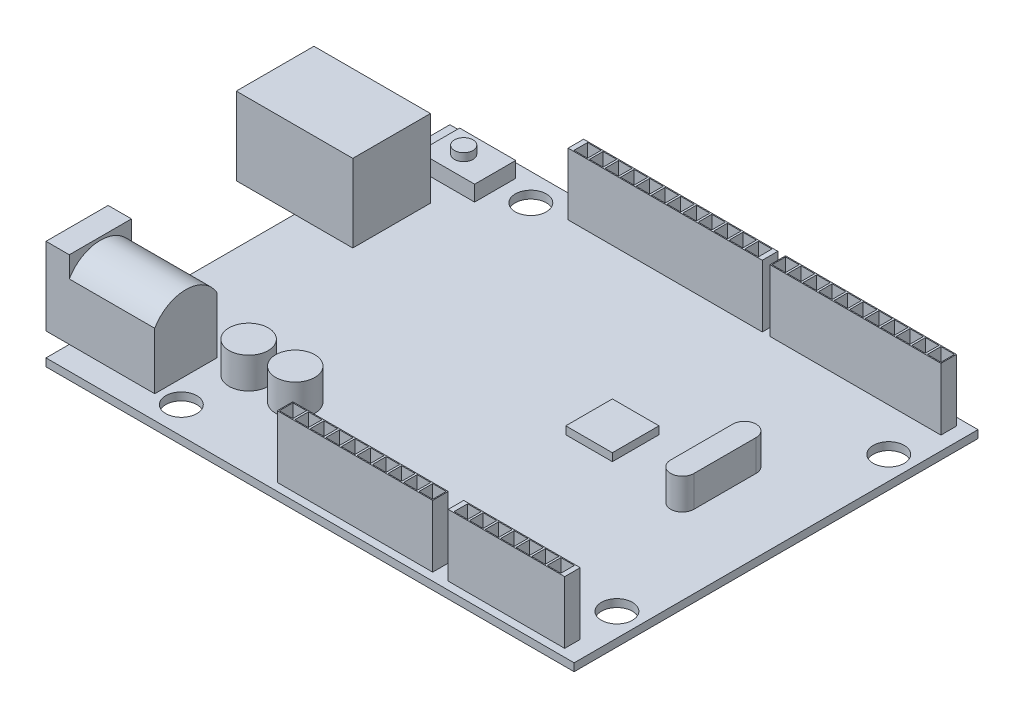
SolidWorks part; units mm, degrees
ref_plane "Front Plane" through (0, 0, 0) normal (0, 0, 1) x (1, 0, 0)
ref_plane "Top Plane" through (0, 0, 0) normal (0, 1, 0) x (1, 0, 0)
ref_plane "Right Plane" through (0, 0, 0) normal (1, 0, 0) x (0, 0, -1)
sketch "Sketch1" plane through (0, 0, 0) normal (0, 1, 0) x (1, 0, 0)
  line L1 (-34, -26) -> (34, -26)
  line L2 (-34, -26) -> (-34, 26)
  line L3 (-34, 26) -> (34, 26)
  line L4 (34, -26) -> (34, 26)
  line L5 (-34, -26) -> (34, 26) construction
  line L6 (-34, 26) -> (34, -26) construction
  point P0 (0, 0)
  dimension "D1" = 68
  dimension "D2" = 52
extrude "Boss-Extrude1" add sketch "Sketch1" along normal blind 1
sketch "Sketch2" plane through (0, 1, 0) normal (0, 1, 0) x (1, 0, 0)
  line L0 (-43.6291, 0) -> (45.0505, 0) construction
  line L1 (-34, 26) -> (-34, -26) construction
  line L2 (-41.5, 16) -> (-26.5, 16)
  line L3 (-41.5, 16) -> (-41.5, 6)
  line L4 (-41.5, 6) -> (-26.5, 6)
  line L5 (-26.5, 16) -> (-26.5, 6)
  line L6 (-41.5, 16) -> (-26.5, 6) construction
  line L7 (-41.5, 6) -> (-26.5, 16) construction
  line L8 (34, 26) -> (-34, 26) construction
  point P3 (-34, 11)
  dimension "D1" = 15
  dimension "D2" = 10
  dimension "D3" = 15
extrude "Boss-Extrude2" add sketch "Sketch2" along normal blind 10
sketch "Sketch3" plane through (-41.5, 0, 0) normal (-1, 0, 0) x (0, 0, 1)
  line L0 (-16, 11) -> (-6, 11) construction
  line L1 (-15, 1.6714) -> (-7, 1.6714)
  line L2 (-15, 1.6714) -> (-15, 9.3286)
  line L3 (-14, 10.3286) -> (-8, 10.3286)
  line L4 (-7, 1.6714) -> (-7, 9.3286)
  line L5 (-15, 1.6714) -> (-7, 10.3286) construction
  line L6 (-15, 10.3286) -> (-7, 1.6714) construction
  line L7 (-7, 9.3286) -> (-8, 10.3286)
  line L8 (-15, 9.3286) -> (-14, 10.3286)
  point P0 (-11, 6)
  point P7 (0, 0)
  point P8 (-11, 11)
  dimension "D1" = 8
extrude "Cut-Extrude1" cut sketch "Sketch3" against normal blind 12
sketch "Sketch4" plane through (-29.5, 0, 0) normal (-1, 0, 0) x (0, 0, 1)
  line L0 (-16, 1) -> (-6, 1) construction
  line L1 (-14, 4) -> (-8, 4)
  line L2 (-14, 4) -> (-14, 7)
  line L3 (-14, 7) -> (-8, 7)
  line L4 (-8, 4) -> (-8, 7)
  line L5 (-14, 4) -> (-8, 7) construction
  line L6 (-14, 7) -> (-8, 4) construction
  line L7 (-7, 1.6714) -> (-7, 9.3286) construction
  point P0 (-11, 5.5)
  point P5 (-11, 4)
  point P8 (-11, 1)
  point P9 (0, 0)
  point P10 (0, 0)
  point P13 (-7, 5.5)
  point P14 (-11, 5.5)
  dimension "D1" = 6
  dimension "D2" = 3
extrude "Boss-Extrude3" add sketch "Sketch4" along normal blind 12
sketch "Sketch5" plane through (0, 1, 0) normal (0, 1, 0) x (1, 0, 0)
  line L0 (-34, -26) -> (34, -26) construction
  line L1 (-23, -23) -> (-37, -23)
  line L2 (-23, -23) -> (-23, -15)
  line L3 (-23, -15) -> (-37, -15)
  line L4 (-37, -23) -> (-37, -15)
  line L5 (-23, -23) -> (-37, -15) construction
  line L6 (-23, -15) -> (-37, -23) construction
  line L7 (-34, 6) -> (-34, -26) construction
  point P0 (-30, -19)
  dimension "D1" = 14
  dimension "D2" = 8
  dimension "D3" = 3
  dimension "D4" = 3
extrude "Boss-Extrude4" add sketch "Sketch5" along normal blind 10
sketch "Sketch7" plane through (-23, 0, 0) normal (1, 0, 0) x (0, 0, -1)
  line L0 (-23.0157, 8.2732) -> (-27.545, 8.2732)
  line L1 (-27.545, 8.2732) -> (-27.545, 16.3206)
  line L2 (-27.545, 16.3206) -> (-10.3117, 16.3206)
  line L3 (-10.3117, 16.3206) -> (-10.3117, 8.2732)
  line L4 (-10.3117, 8.2732) -> (-14.9843, 8.2732)
  arc A0 (-14.9843, 8.2732) -> (-23.0157, 8.2732) centre (-19, 6) ccw
extrude "Cut-Extrude3" cut sketch "Sketch7" against normal up to surface (11 mm away) up to face at (-34, 0.75, 2)
sketch "Sketch8" plane through (-37, 0, 0) normal (-1, 0, 0) x (0, 0, 1)
  circle A0 centre (19, 6) radius 3
  dimension "D1" = 6
extrude "Cut-Extrude4" cut sketch "Sketch8" against normal blind 10
sketch "Sketch9" plane through (-27, 0, 0) normal (-1, 0, 0) x (0, 0, 1)
  circle A0 centre (19, 6) radius 0.5
  dimension "D1" = 1
extrude "Boss-Extrude5" add sketch "Sketch9" along normal blind 10
sketch "Sketch10" plane through (0, 1, 0) normal (0, 1, 0) x (1, 0, 0)
  line L0 (-34, 26) -> (-34, 16) construction
  line L1 (-31, 24.2587) -> (-23.7766, 24.2587)
  line L2 (-31, 24.2587) -> (-31, 18.9615)
  line L3 (-31, 18.9615) -> (-23.7766, 18.9615)
  line L4 (-23.7766, 24.2587) -> (-23.7766, 18.9615)
  line L5 (-31, 24.2587) -> (-23.7766, 18.9615) construction
  line L6 (-31, 18.9615) -> (-23.7766, 24.2587) construction
  point P0 (-27.3883, 21.6101)
  dimension "D1" = 3
extrude "Boss-Extrude6" add sketch "Sketch10" along normal blind 2
sketch "Sketch11" plane through (0, 3, 0) normal (0, 1, 0) x (1, 0, 0)
  circle A0 centre (-27.8281, 21.6101) radius 1.1922
extrude "Boss-Extrude7" add sketch "Sketch11" along normal blind 1
sketch "Sketch12" plane through (0, 1, 0) normal (0, 1, 0) x (1, 0, 0)
  circle A0 centre (-19.0396, -14.8682) radius 2.5282
  circle A1 centre (-13.0396, -14.8682) radius 2.5282
  dimension "D1" = 6
extrude "Boss-Extrude8" add sketch "Sketch12" along normal blind 4
sketch "Sketch13" plane through (0, 1, 0) normal (0, 1, 0) x (1, 0, 0)
  line L0 (-23.7766, 18.9615) -> (-23.7766, 24.2587) construction
  line L1 (9.2234, 25) -> (-15.7766, 25)
  line L2 (9.2234, 25) -> (9.2234, 23)
  line L3 (9.2234, 23) -> (-15.7766, 23)
  line L4 (-15.7766, 25) -> (-15.7766, 23)
  line L5 (9.2234, 25) -> (-15.7766, 23) construction
  line L6 (9.2234, 23) -> (-15.7766, 25) construction
  line L7 (10.2234, 25) -> (32.2234, 25)
  line L8 (10.2234, 25) -> (10.2234, 23)
  line L9 (10.2234, 23) -> (32.2234, 23)
  line L10 (32.2234, 25) -> (32.2234, 23)
  line L11 (10.2234, 25) -> (32.2234, 23) construction
  line L12 (10.2234, 23) -> (32.2234, 25) construction
  line L13 (34, 26) -> (-34, 26) construction
  point P0 (-3.2766, 24)
  point P5 (21.2234, 24)
  dimension "D1" = 25
  dimension "D2" = 8
  dimension "D3" = 2
  dimension "D4" = 1
  dimension "D5" = 2
  dimension "D6" = 1
  dimension "D7" = 22
  dimension "D8" = 1
extrude "Boss-Extrude9" add sketch "Sketch13" along normal blind 8
sketch "Sketch14" plane through (0, 1, 0) normal (0, 1, 0) x (1, 0, 0)
  line L0 (-34, -26) -> (34, -26) construction
  line L1 (16.7836, -23) -> (31.7836, -23)
  line L2 (16.7836, -23) -> (16.7836, -25)
  line L3 (16.7836, -25) -> (31.7836, -25)
  line L4 (31.7836, -23) -> (31.7836, -25)
  line L5 (16.7836, -23) -> (31.7836, -25) construction
  line L6 (16.7836, -25) -> (31.7836, -23) construction
  line L7 (-5.2164, -23) -> (14.7836, -23)
  line L8 (-5.2164, -23) -> (-5.2164, -25)
  line L9 (-5.2164, -25) -> (14.7836, -25)
  line L10 (14.7836, -23) -> (14.7836, -25)
  line L11 (-5.2164, -23) -> (14.7836, -25) construction
  line L12 (-5.2164, -25) -> (14.7836, -23) construction
  point P0 (24.2836, -24)
  point P5 (4.7836, -24)
  dimension "D1" = 15
  dimension "D2" = 2
  dimension "D3" = 1
  dimension "D4" = 2
  dimension "D5" = 2
  dimension "D6" = 1
  dimension "D7" = 20
extrude "Boss-Extrude10" add sketch "Sketch14" along normal blind 8
sketch "Sketch15" plane through (0, 9, 0) normal (0, 1, 0) x (1, 0, 0)
  line L0 (-15.7766, 25) -> (-15.7766, 23) construction
  line L1 (-15.1516, 24.875) -> (-13.4016, 24.875)
  line L2 (-15.1516, 24.875) -> (-15.1516, 23.125)
  line L3 (-15.1516, 23.125) -> (-13.4016, 23.125)
  line L4 (-13.4016, 24.875) -> (-13.4016, 23.125)
  line L5 (-15.1516, 24.875) -> (-13.4016, 23.125) construction
  line L6 (-15.1516, 23.125) -> (-13.4016, 24.875) construction
  line L7 (-13.1516, 24.875) -> (-13.1516, 23.125)
  line L8 (-13.1516, 24.875) -> (-11.4016, 24.875)
  line L9 (-11.4016, 24.875) -> (-11.4016, 23.125)
  line L10 (-13.1516, 23.125) -> (-11.4016, 23.125)
  line L11 (-11.1516, 24.875) -> (-11.1516, 23.125)
  line L12 (-11.1516, 24.875) -> (-9.4016, 24.875)
  line L13 (-9.4016, 24.875) -> (-9.4016, 23.125)
  line L14 (-11.1516, 23.125) -> (-9.4016, 23.125)
  line L15 (-9.1516, 24.875) -> (-9.1516, 23.125)
  line L16 (-9.1516, 24.875) -> (-7.4016, 24.875)
  line L17 (-7.4016, 24.875) -> (-7.4016, 23.125)
  line L18 (-9.1516, 23.125) -> (-7.4016, 23.125)
  line L19 (-7.1516, 24.875) -> (-7.1516, 23.125)
  line L20 (-7.1516, 24.875) -> (-5.4016, 24.875)
  line L21 (-5.4016, 24.875) -> (-5.4016, 23.125)
  line L22 (-7.1516, 23.125) -> (-5.4016, 23.125)
  line L23 (-5.1516, 24.875) -> (-5.1516, 23.125)
  line L24 (-5.1516, 24.875) -> (-3.4016, 24.875)
  line L25 (-3.4016, 24.875) -> (-3.4016, 23.125)
  line L26 (-5.1516, 23.125) -> (-3.4016, 23.125)
  line L27 (-3.1516, 24.875) -> (-3.1516, 23.125)
  line L28 (-3.1516, 24.875) -> (-1.4016, 24.875)
  line L29 (-1.4016, 24.875) -> (-1.4016, 23.125)
  line L30 (-3.1516, 23.125) -> (-1.4016, 23.125)
  line L31 (-1.1516, 24.875) -> (-1.1516, 23.125)
  line L32 (-1.1516, 24.875) -> (0.5984, 24.875)
  line L33 (0.5984, 24.875) -> (0.5984, 23.125)
  line L34 (-1.1516, 23.125) -> (0.5984, 23.125)
  line L35 (0.8484, 24.875) -> (0.8484, 23.125)
  line L36 (0.8484, 24.875) -> (2.5984, 24.875)
  line L37 (2.5984, 24.875) -> (2.5984, 23.125)
  line L38 (0.8484, 23.125) -> (2.5984, 23.125)
  line L39 (2.8484, 24.875) -> (2.8484, 23.125)
  line L40 (2.8484, 24.875) -> (4.5984, 24.875)
  line L41 (4.5984, 24.875) -> (4.5984, 23.125)
  line L42 (2.8484, 23.125) -> (4.5984, 23.125)
  line L43 (4.8484, 24.875) -> (4.8484, 23.125)
  line L44 (4.8484, 24.875) -> (6.5984, 24.875)
  line L45 (6.5984, 24.875) -> (6.5984, 23.125)
  line L46 (4.8484, 23.125) -> (6.5984, 23.125)
  line L47 (6.8484, 24.875) -> (6.8484, 23.125)
  line L48 (6.8484, 24.875) -> (8.5984, 24.875)
  line L49 (8.5984, 24.875) -> (8.5984, 23.125)
  line L50 (6.8484, 23.125) -> (8.5984, 23.125)
  point P0 (-14.2766, 24)
  point P8 (-15.7766, 24)
  dimension "D1" = 1.75
  dimension "D2" = 1.5
  dimension "D3" = 12
extrude "Cut-Extrude5" cut sketch "Sketch15" against normal blind 7
sketch "Sketch16" plane through (0, 9, 0) normal (0, 1, 0) x (1, 0, 0)
  line L0 (10.2234, 25) -> (10.2234, 23) construction
  line L1 (10.3484, 24.875) -> (12.0984, 24.875)
  line L2 (10.3484, 24.875) -> (10.3484, 23.125)
  line L3 (10.3484, 23.125) -> (12.0984, 23.125)
  line L4 (12.0984, 24.875) -> (12.0984, 23.125)
  line L5 (10.3484, 24.875) -> (12.0984, 23.125) construction
  line L6 (10.3484, 23.125) -> (12.0984, 24.875) construction
  line L7 (10.2234, 25) -> (10.2234, 23) construction
  line L8 (12.3484, 24.875) -> (12.3484, 23.125)
  line L9 (12.3484, 24.875) -> (14.0984, 24.875)
  line L10 (14.0984, 24.875) -> (14.0984, 23.125)
  line L11 (12.3484, 23.125) -> (14.0984, 23.125)
  line L12 (14.3484, 24.875) -> (14.3484, 23.125)
  line L13 (14.3484, 24.875) -> (16.0984, 24.875)
  line L14 (16.0984, 24.875) -> (16.0984, 23.125)
  line L15 (14.3484, 23.125) -> (16.0984, 23.125)
  line L16 (16.3484, 24.875) -> (16.3484, 23.125)
  line L17 (16.3484, 24.875) -> (18.0984, 24.875)
  line L18 (18.0984, 24.875) -> (18.0984, 23.125)
  line L19 (16.3484, 23.125) -> (18.0984, 23.125)
  line L20 (18.3484, 24.875) -> (18.3484, 23.125)
  line L21 (18.3484, 24.875) -> (20.0984, 24.875)
  line L22 (20.0984, 24.875) -> (20.0984, 23.125)
  line L23 (18.3484, 23.125) -> (20.0984, 23.125)
  line L24 (20.3484, 24.875) -> (20.3484, 23.125)
  line L25 (20.3484, 24.875) -> (22.0984, 24.875)
  line L26 (22.0984, 24.875) -> (22.0984, 23.125)
  line L27 (20.3484, 23.125) -> (22.0984, 23.125)
  line L28 (22.3484, 24.875) -> (22.3484, 23.125)
  line L29 (22.3484, 24.875) -> (24.0984, 24.875)
  line L30 (24.0984, 24.875) -> (24.0984, 23.125)
  line L31 (22.3484, 23.125) -> (24.0984, 23.125)
  line L32 (24.3484, 24.875) -> (24.3484, 23.125)
  line L33 (24.3484, 24.875) -> (26.0984, 24.875)
  line L34 (26.0984, 24.875) -> (26.0984, 23.125)
  line L35 (24.3484, 23.125) -> (26.0984, 23.125)
  line L36 (26.3484, 24.875) -> (26.3484, 23.125)
  line L37 (26.3484, 24.875) -> (28.0984, 24.875)
  line L38 (28.0984, 24.875) -> (28.0984, 23.125)
  line L39 (26.3484, 23.125) -> (28.0984, 23.125)
  line L40 (28.3484, 24.875) -> (28.3484, 23.125)
  line L41 (28.3484, 24.875) -> (30.0984, 24.875)
  line L42 (30.0984, 24.875) -> (30.0984, 23.125)
  line L43 (28.3484, 23.125) -> (30.0984, 23.125)
  line L44 (30.3484, 24.875) -> (30.3484, 23.125)
  line L45 (30.3484, 24.875) -> (32.0984, 24.875)
  line L46 (32.0984, 24.875) -> (32.0984, 23.125)
  line L47 (30.3484, 23.125) -> (32.0984, 23.125)
  point P0 (11.2234, 24)
  point P8 (10.2234, 24)
  dimension "D1" = 1.75
  dimension "D2" = 1
  dimension "D3" = 11
extrude "Cut-Extrude6" cut sketch "Sketch16" against normal blind 7
sketch "Sketch17" plane through (0, 9, 0) normal (0, 1, 0) x (1, 0, 0)
  line L1 (-5.0914, -23.125) -> (-3.3414, -23.125)
  line L2 (-5.0914, -23.125) -> (-5.0914, -24.875)
  line L3 (-5.0914, -24.875) -> (-3.3414, -24.875)
  line L4 (-3.3414, -23.125) -> (-3.3414, -24.875)
  line L5 (-5.0914, -23.125) -> (-3.3414, -24.875) construction
  line L6 (-5.0914, -24.875) -> (-3.3414, -23.125) construction
  line L7 (-5.2164, -23) -> (-5.2164, -25) construction
  line L8 (-3.0914, -23.125) -> (-3.0914, -24.875)
  line L9 (-3.0914, -23.125) -> (-1.3414, -23.125)
  line L10 (-1.3414, -23.125) -> (-1.3414, -24.875)
  line L11 (-3.0914, -24.875) -> (-1.3414, -24.875)
  line L12 (-1.0914, -23.125) -> (-1.0914, -24.875)
  line L13 (-1.0914, -23.125) -> (0.6586, -23.125)
  line L14 (0.6586, -23.125) -> (0.6586, -24.875)
  line L15 (-1.0914, -24.875) -> (0.6586, -24.875)
  line L16 (0.9086, -23.125) -> (0.9086, -24.875)
  line L17 (0.9086, -23.125) -> (2.6586, -23.125)
  line L18 (2.6586, -23.125) -> (2.6586, -24.875)
  line L19 (0.9086, -24.875) -> (2.6586, -24.875)
  line L20 (2.9086, -23.125) -> (2.9086, -24.875)
  line L21 (2.9086, -23.125) -> (4.6586, -23.125)
  line L22 (4.6586, -23.125) -> (4.6586, -24.875)
  line L23 (2.9086, -24.875) -> (4.6586, -24.875)
  line L24 (4.9086, -23.125) -> (4.9086, -24.875)
  line L25 (4.9086, -23.125) -> (6.6586, -23.125)
  line L26 (6.6586, -23.125) -> (6.6586, -24.875)
  line L27 (4.9086, -24.875) -> (6.6586, -24.875)
  line L28 (6.9086, -23.125) -> (6.9086, -24.875)
  line L29 (6.9086, -23.125) -> (8.6586, -23.125)
  line L30 (8.6586, -23.125) -> (8.6586, -24.875)
  line L31 (6.9086, -24.875) -> (8.6586, -24.875)
  line L32 (8.9086, -23.125) -> (8.9086, -24.875)
  line L33 (8.9086, -23.125) -> (10.6586, -23.125)
  line L34 (10.6586, -23.125) -> (10.6586, -24.875)
  line L35 (8.9086, -24.875) -> (10.6586, -24.875)
  line L36 (10.9086, -23.125) -> (10.9086, -24.875)
  line L37 (10.9086, -23.125) -> (12.6586, -23.125)
  line L38 (12.6586, -23.125) -> (12.6586, -24.875)
  line L39 (10.9086, -24.875) -> (12.6586, -24.875)
  line L40 (12.9086, -23.125) -> (12.9086, -24.875)
  line L41 (12.9086, -23.125) -> (14.6586, -23.125)
  line L42 (14.6586, -23.125) -> (14.6586, -24.875)
  line L43 (12.9086, -24.875) -> (14.6586, -24.875)
  point P0 (-4.2164, -24)
  point P9 (-5.0914, -24)
  point P11 (-5.2164, -24)
  dimension "D1" = 1.75
  dimension "D2" = 1
  dimension "D3" = 10
extrude "Cut-Extrude7" cut sketch "Sketch17" against normal blind 7
sketch "Sketch18" plane through (0, 9, 0) normal (0, 1, 0) x (1, 0, 0)
  line L0 (16.7836, -23) -> (16.7836, -25) construction
  line L1 (17.4086, -23.125) -> (19.1586, -23.125)
  line L2 (17.4086, -23.125) -> (17.4086, -24.875)
  line L3 (17.4086, -24.875) -> (19.1586, -24.875)
  line L4 (19.1586, -23.125) -> (19.1586, -24.875)
  line L5 (17.4086, -23.125) -> (19.1586, -24.875) construction
  line L6 (17.4086, -24.875) -> (19.1586, -23.125) construction
  line L7 (19.4086, -23.125) -> (19.4086, -24.875)
  line L8 (19.4086, -23.125) -> (21.1586, -23.125)
  line L9 (21.1586, -23.125) -> (21.1586, -24.875)
  line L10 (19.4086, -24.875) -> (21.1586, -24.875)
  line L11 (21.4086, -23.125) -> (21.4086, -24.875)
  line L12 (21.4086, -23.125) -> (23.1586, -23.125)
  line L13 (23.1586, -23.125) -> (23.1586, -24.875)
  line L14 (21.4086, -24.875) -> (23.1586, -24.875)
  line L15 (23.4086, -23.125) -> (23.4086, -24.875)
  line L16 (23.4086, -23.125) -> (25.1586, -23.125)
  line L17 (25.1586, -23.125) -> (25.1586, -24.875)
  line L18 (23.4086, -24.875) -> (25.1586, -24.875)
  line L19 (25.4086, -23.125) -> (25.4086, -24.875)
  line L20 (25.4086, -23.125) -> (27.1586, -23.125)
  line L21 (27.1586, -23.125) -> (27.1586, -24.875)
  line L22 (25.4086, -24.875) -> (27.1586, -24.875)
  line L23 (27.4086, -23.125) -> (27.4086, -24.875)
  line L24 (27.4086, -23.125) -> (29.1586, -23.125)
  line L25 (29.1586, -23.125) -> (29.1586, -24.875)
  line L26 (27.4086, -24.875) -> (29.1586, -24.875)
  line L27 (29.4086, -23.125) -> (29.4086, -24.875)
  line L28 (29.4086, -23.125) -> (31.1586, -23.125)
  line L29 (31.1586, -23.125) -> (31.1586, -24.875)
  line L30 (29.4086, -24.875) -> (31.1586, -24.875)
  point P0 (18.2836, -24)
  point P8 (16.7836, -24)
  dimension "D1" = 1.75
  dimension "D2" = 1.5
  dimension "D3" = 7
extrude "Cut-Extrude8" cut sketch "Sketch18" against normal blind 7
sketch "Sketch19" plane through (0, 1, 0) normal (0, 1, 0) x (1, 0, 0)
  line L0 (23.0971, -1.1708) -> (23.0971, 6.8292) construction
  line L1 (21.5971, -1.1708) -> (21.5971, 6.8292)
  line L2 (24.5971, -1.1708) -> (24.5971, 6.8292)
  arc A0 (21.5971, -1.1708) -> (24.5971, -1.1708) centre (23.0971, -1.1708) ccw
  arc A1 (24.5971, 6.8292) -> (21.5971, 6.8292) centre (23.0971, 6.8292) ccw
  point P2 (23.0971, 2.8292)
  point P7 (22.9767, 4.9962)
  point P8 (0, 0)
  point P9 (23.0971, 2.8292)
  point P10 (0, 0)
  dimension "D1" = 3
  dimension "D2" = 8
extrude "Boss-Extrude11" add sketch "Sketch19" along normal blind 4
sketch "Sketch20" plane through (0, 1, 0) normal (0, 1, 0) x (1, 0, 0)
  line L1 (8.0354, 4.8865) -> (14.0354, 4.8865)
  line L2 (8.0354, 4.8865) -> (8.0354, -1.1135)
  line L3 (8.0354, -1.1135) -> (14.0354, -1.1135)
  line L4 (14.0354, 4.8865) -> (14.0354, -1.1135)
  line L5 (8.0354, 4.8865) -> (14.0354, -1.1135) construction
  line L6 (8.0354, -1.1135) -> (14.0354, 4.8865) construction
  point P0 (11.0354, 1.8865)
  point P5 (11.0354, 1.8865)
  dimension "D1" = 6
  dimension "D2" = 6
extrude "Boss-Extrude12" add sketch "Sketch20" along normal blind 1
sketch "Sketch21" plane through (0, 1, 0) normal (0, 1, 0) x (1, 0, 0)
  line L0 (-45.1446, 0) -> (41.8718, 0) construction
  circle A0 centre (-20.0752, 22.5) radius 2
  circle A1 centre (-20.0752, -22.5) radius 2
  circle A2 centre (31.0101, -17.5) radius 2
  circle A3 centre (31.0101, 17.5) radius 2
  dimension "D1" = 4
  dimension "D2" = 45
  dimension "D3" = 35
extrude "Cut-Extrude9" cut sketch "Sketch21" against normal through all
